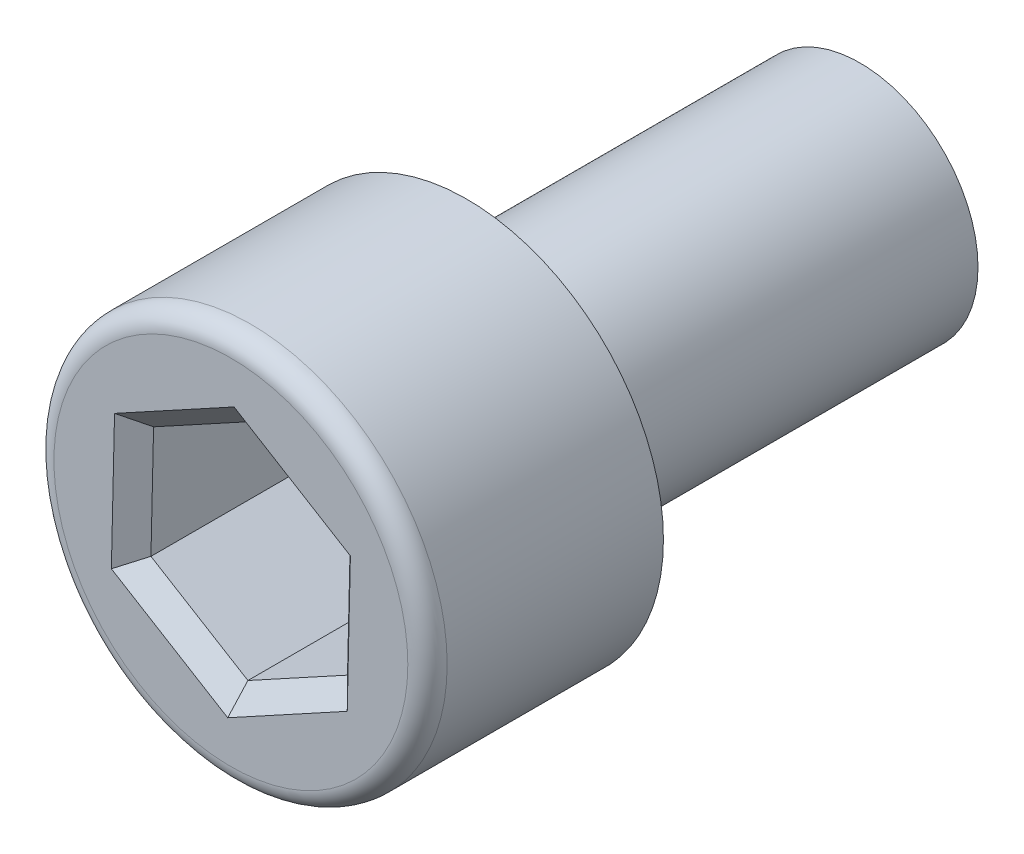
SolidWorks part; units mm, degrees
material "Alloy Steel"
ref_plane "Front" through (0, 0, 0) normal (0, 0, 1) x (1, 0, 0)
ref_plane "Top" through (0, 0, 0) normal (0, 1, 0) x (1, 0, 0)
ref_plane "Right" through (0, 0, 0) normal (1, 0, 0) x (0, 0, -1)
sketch "Sketch2" plane through (0, 0, 0) normal (0, 0, 1) x (1, 0, 0)
  circle A0 centre (0, 0) radius 3
  dimension "D1" = 6
extrude "Extrude1" add sketch "Sketch2" against normal blind 10
sketch "Sketch3" plane through (0, 0, 0) normal (0, 0, 1) x (1, 0, 0)
  circle A0 centre (0, 0) radius 5
  dimension "D1" = 10
extrude "Extrude2" add sketch "Sketch3" along normal blind 6
sketch "Sketch4" plane through (0, 0, 6) normal (0, 0, 1) x (1, 0, 0)
  line L1 (-2.4657, 1.5012) -> (-2.533, -1.3847)
  line L2 (-2.533, -1.3847) -> (-0.0673, -2.886)
  line L3 (-0.0673, -2.886) -> (2.4657, -1.5012)
  line L4 (2.4657, -1.5012) -> (2.533, 1.3847)
  line L5 (2.533, 1.3847) -> (0.0673, 2.886)
  line L6 (0.0673, 2.886) -> (-2.4657, 1.5012)
  circle A0 centre (0, 0) radius 2.5 construction
  dimension "D1" = 5
extrude "Cut-Extrude1" cut sketch "Sketch4" against normal blind 6
fillet "Fillet1" radius 0.5 1 edges at (5, 0, 6)
chamfer "Chamfer1" distance 0.5 angle 45 6 edges at (-2.4993, 0.0583, 6) (-1.3001, -2.1353, 6) (1.1992, -2.1936, 6) (2.4993, -0.0583, 6) (1.3001, 2.1353, 6) (-1.1992, 2.1936, 6)
